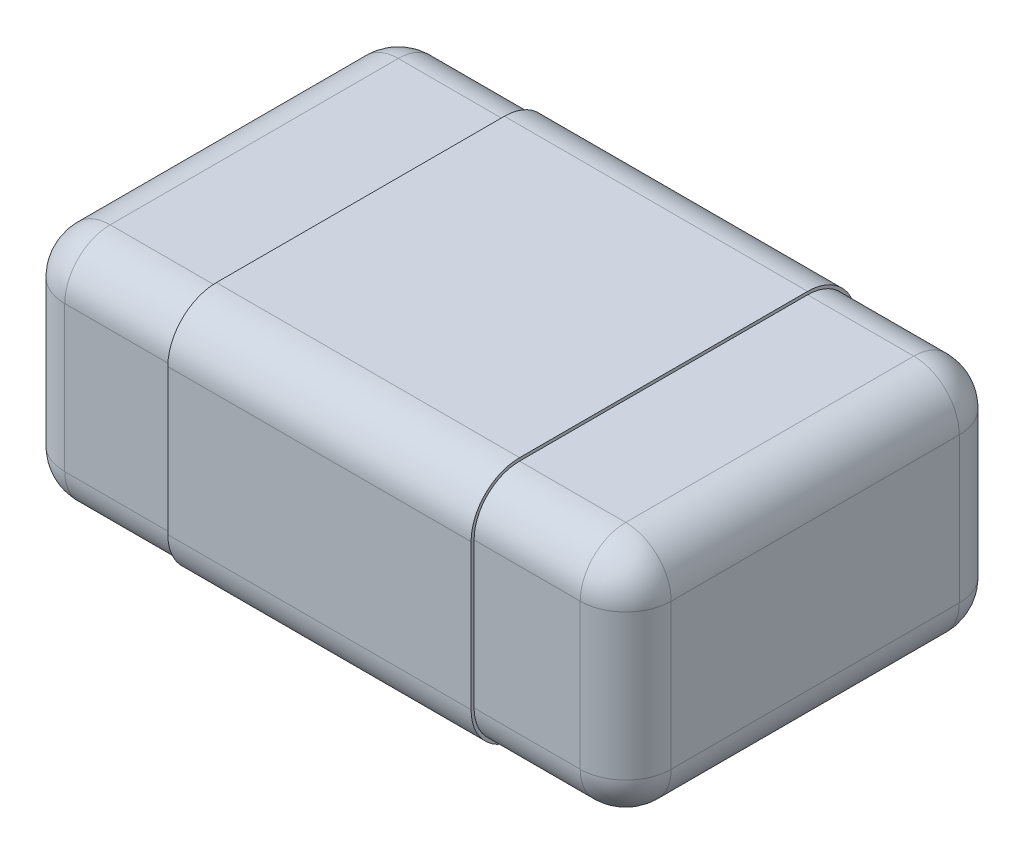
SolidWorks part; units mm, degrees
material "Aço inoxidável fundido"
ref_plane "Plano frontal" through (0, 0, 0) normal (0, 0, 1) x (1, 0, 0)
ref_plane "Plano superior" through (0, 0, 0) normal (0, 1, 0) x (1, 0, 0)
ref_plane "Plano direito" through (0, 0, 0) normal (1, 0, 0) x (0, 0, -1)
sketch "Esboço1" plane through (0, 0, 0) normal (0, 1, 0) x (1, 0, 0)
  line L0 (-1, -0.625) -> (1, -0.625)
  line L1 (1, -0.625) -> (1, 0.625)
  line L2 (1, 0.625) -> (-1, 0.625)
  line L3 (-1, 0.625) -> (-1, -0.625)
extrude "Ressalto-extrusão1" add sketch "Esboço1" against normal blind 0.78
fillet "Filete1" radius 0.15 12 edges at (0, -0.78, -0.625) (-1, -0.39, -0.625) (1, -0.39, -0.625) (0, 0, -0.625) (-1, -0.78, 0) (1, -0.78, 0) (0, -0.78, 0.625) (-1, 0, 0) (1, 0, 0) (-1, -0.39, 0.625) (1, -0.39, 0.625) (0, 0, 0.625)
sketch "Esboço4" plane through (0, 0, 0) normal (1, 0, 0) x (0, 0, -1)
  line L0 (0.625, -0.63) -> (0.625, -0.15) construction
  line L1 (0.625, -0.63) -> (0.625, -0.15)
  line L2 (0.475, -0.78) -> (-0.475, -0.78) construction
  line L3 (0.475, -0.78) -> (-0.475, -0.78)
  line L4 (0.475, 0) -> (-0.475, 0) construction
  line L5 (-0.625, -0.15) -> (-0.625, -0.63) construction
  line L6 (0.475, 0) -> (-0.475, 0)
  line L7 (-0.625, -0.15) -> (-0.625, -0.63)
  line L8 (0.635, -0.63) -> (0.635, -0.15)
  line L9 (0.475, 0.01) -> (-0.475, 0.01)
  line L10 (-0.635, -0.15) -> (-0.635, -0.63)
  line L11 (0.475, -0.79) -> (-0.475, -0.79)
  arc A5 (0.475, -0.78) -> (0.625, -0.63) centre (0.475, -0.63) ccw construction
  arc A6 (0.475, -0.78) -> (0.625, -0.63) centre (0.475, -0.63) ccw
  arc A7 (-0.475, 0) -> (-0.625, -0.15) centre (-0.475, -0.15) ccw construction
  arc A8 (-0.625, -0.63) -> (-0.475, -0.78) centre (-0.475, -0.63) ccw construction
  arc A9 (-0.475, 0) -> (-0.625, -0.15) centre (-0.475, -0.15) ccw
  arc A10 (-0.625, -0.63) -> (-0.475, -0.78) centre (-0.475, -0.63) ccw
  arc A11 (0.625, -0.15) -> (0.475, 0) centre (0.475, -0.15) ccw construction
  arc A12 (0.625, -0.15) -> (0.475, 0) centre (0.475, -0.15) ccw
  arc A13 (0.635, -0.15) -> (0.475, 0.01) centre (0.475, -0.15) ccw
  arc A14 (-0.475, 0.01) -> (-0.635, -0.15) centre (-0.475, -0.15) ccw
  arc A15 (-0.635, -0.63) -> (-0.475, -0.79) centre (-0.475, -0.63) ccw
  arc A16 (0.475, -0.79) -> (0.635, -0.63) centre (0.475, -0.63) ccw
  dimension "D1" = 0.01
extrude "Ressalto-extrusão4" add sketch "Esboço4" along normal blind 0.5 and the other way blind 0.5
sketch "Esboço2" plane through (0, -0.79, 0) normal (0, -1, 0) x (0, 0, 1)
  line L1 (-0.475, 0.5) -> (0.475, 0.5) construction
  line L2 (-0.475, -0.5) -> (0.475, -0.5) construction
  line L7 (0.2404, -0.5) -> (0.2404, 0.5) construction
  text T0 "<b>822</b>\r\n\r\n" font "Tahoma" height 0.5
extrude "Ressalto-extrusão5" add sketch "Esboço2" along normal blind 0.02
